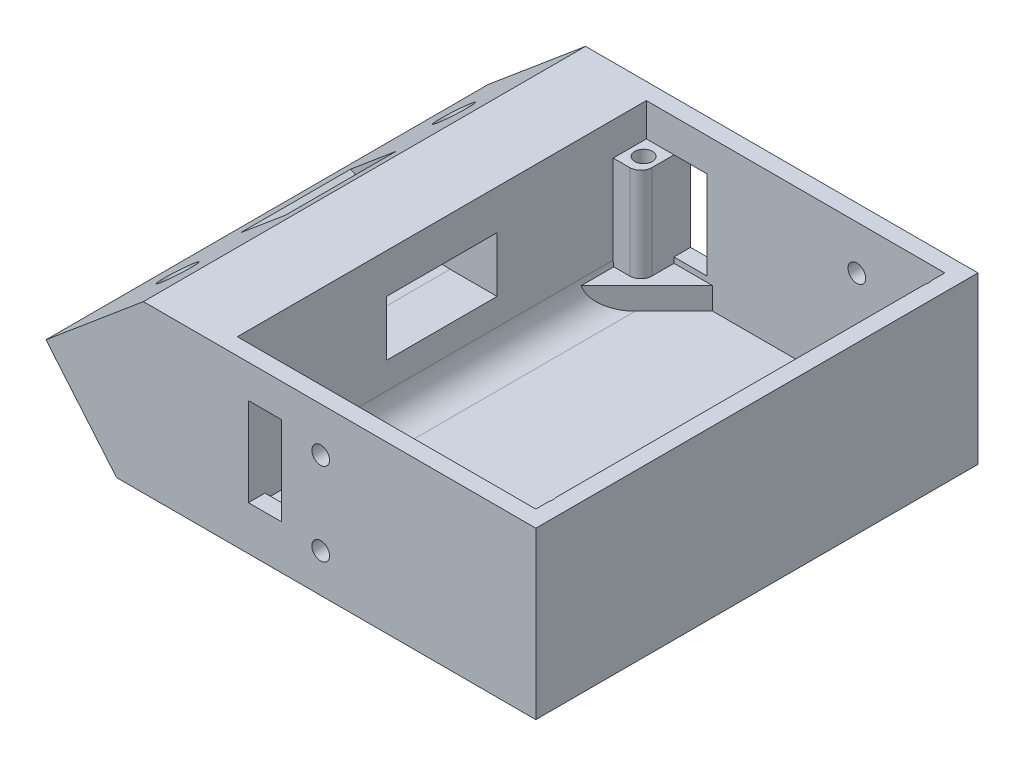
SolidWorks part; units mm, degrees
ref_plane "Спереди" through (0, 0, 0) normal (0, 0, 1) x (1, 0, 0)
ref_plane "Сверху" through (0, 0, 0) normal (0, 1, 0) x (1, 0, 0)
ref_plane "Справа" through (0, 0, 0) normal (1, 0, 0) x (0, 0, -1)
sketch "Sketch1" plane through (0, 0, 0) normal (0, 1, 0) x (1, 0, 0)
  line L1 (30.5, -40) -> (-30.5, -40)
  line L2 (30.5, -40) -> (30.5, 40)
  line L3 (30.5, 40) -> (-30.5, 40)
  line L4 (-30.5, -40) -> (-30.5, 40)
  line L5 (30.5, -40) -> (-30.5, 40) construction
  line L6 (30.5, 40) -> (-30.5, -40) construction
  point P0 (0, 0)
  dimension "D1" = 80
  dimension "D2" = 61
extrude "Boss-Extrude1" add sketch "Sketch1" along normal blind 30
sketch "Sketch2" plane through (0, 30, 0) normal (0, 1, 0) x (1, 0, 0)
  line L0 (30.5, 40) -> (-30.5, 40) construction
  line L1 (-26.5, -37) -> (27.5, -37)
  line L2 (-26.5, -37) -> (-26.5, 37)
  line L3 (-26.5, 37) -> (27.5, 37)
  line L4 (27.5, -37) -> (27.5, 37)
  line L5 (-30.5, -40) -> (30.5, -40) construction
  line L6 (-30.5, 40) -> (-30.5, -40) construction
  line L7 (30.5, -40) -> (30.5, 40) construction
  point P0 (0, 0)
  dimension "D1" = 3
  dimension "D2" = 3
  dimension "D3" = 3
  dimension "D4" = 4
extrude "Cut-Extrude1" cut sketch "Sketch2" against normal blind 27
sketch "Sketch11" plane through (0, 0, 40) normal (0, 0, 1) x (1, 0, 0)
  line L0 (-30.5, 30) -> (-40.5, 30)
  line L1 (-30.5, 0) -> (-58.119, 0)
  line L2 (-30.5, 0) -> (-30.5, 30)
  line L3 (-58.119, 0) -> (-58.119, 15.2159)
  line L4 (-40.5, 30) -> (-58.119, 15.2159)
  line L5 (-40.5, 30) -> (-40.5, 0) construction
  dimension "D1" = 23
  dimension "D2" = 50
  dimension "D3" = 10
extrude "Boss-Extrude3" add sketch "Sketch11" against normal up to surface (80 mm away) up to face at (0, 15, -40)
sketch "Sketch7" plane through (0, 3, 0) normal (0, 1, 0) x (1, 0, 0)
  line L0 (27.5, -25) -> (15.5, -37)
  line L1 (27.5, -37) -> (27.5, 37) construction
  line L2 (-26.5, -37) -> (27.5, -37) construction
  line L3 (15.5, -37) -> (27.5, -37)
  line L4 (27.5, -37) -> (27.5, -25)
  line L5 (27.5, 25) -> (15.5, 37)
  line L6 (27.5, 37) -> (-26.5, 37) construction
  line L7 (15.5, 37) -> (27.5, 37)
  line L8 (27.5, 37) -> (27.5, 25)
  line L9 (-26.5, 25) -> (-14.5, 37)
  line L10 (-26.5, 37) -> (-26.5, -37) construction
  line L11 (-14.5, 37) -> (-26.5, 37)
  line L12 (-26.5, 37) -> (-26.5, 25)
  line L13 (-14.5, -37) -> (-26.5, -25)
  line L14 (-26.5, 37) -> (-26.5, -37) construction
  line L15 (-26.5, -25) -> (-26.5, -37)
  line L16 (-26.5, -37) -> (-14.5, -37)
  dimension "D1" = 12
extrude "Boss-Extrude2" add sketch "Sketch7" along normal blind 4
sketch "Sketch5" plane through (0, 0, 0) normal (0, -1, 0) x (1, 0, 0)
  line L0 (1, -40) -> (1, 40) construction
  line L1 (30.5, -40) -> (-58.119, -40) construction
  line L2 (-58.119, 40) -> (30.5, 40) construction
  line L4 (26, 34) -> (-24, 34) construction
  line L5 (26, 34) -> (26, -34) construction
  line L6 (26, -34) -> (-24, -34) construction
  line L7 (-24, 34) -> (-24, -34) construction
  line L8 (26, 34) -> (-24, -34) construction
  line L9 (26, -34) -> (-24, 34) construction
  circle A0 centre (-24, -34) radius 1.6
  circle A1 centre (-24, 34) radius 1.6
  circle A2 centre (26, 34) radius 1.6
  circle A3 centre (26, -34) radius 1.6
  point P6 (1, 0)
  dimension "D4" = 3.2
  dimension "D1" = 68
  dimension "D2" = 50
  dimension "D3" = 1
extrude "Cut-Extrude3" cut sketch "Sketch5" against normal through all
sketch "Sketch8" plane through (0, 0, 0) normal (0, -1, 0) x (1, 0, 0)
  line L0 (30.5, -40) -> (-58.119, -40) construction
  line L1 (-25.625, 36.8146) -> (-27.25, 34)
  line L2 (-27.25, 34) -> (-25.625, 31.1854)
  line L3 (-25.625, 31.1854) -> (-22.375, 31.1854)
  line L4 (-22.375, 31.1854) -> (-20.75, 34)
  line L5 (-20.75, 34) -> (-22.375, 36.8146)
  line L6 (-22.375, 36.8146) -> (-25.625, 36.8146)
  line L7 (24.375, 36.8146) -> (22.75, 34)
  line L8 (22.75, 34) -> (24.375, 31.1854)
  line L9 (24.375, 31.1854) -> (27.625, 31.1854)
  line L10 (27.625, 31.1854) -> (29.25, 34)
  line L11 (29.25, 34) -> (27.625, 36.8146)
  line L12 (27.625, 36.8146) -> (24.375, 36.8146)
  line L13 (-25.625, -31.1854) -> (-27.25, -34)
  line L14 (-27.25, -34) -> (-25.625, -36.8146)
  line L15 (-25.625, -36.8146) -> (-22.375, -36.8146)
  line L16 (-22.375, -36.8146) -> (-20.75, -34)
  line L17 (-20.75, -34) -> (-22.375, -31.1854)
  line L18 (-22.375, -31.1854) -> (-25.625, -31.1854)
  line L19 (24.375, -31.1854) -> (22.75, -34)
  line L20 (22.75, -34) -> (24.375, -36.8146)
  line L21 (24.375, -36.8146) -> (27.625, -36.8146)
  line L22 (27.625, -36.8146) -> (29.25, -34)
  line L23 (29.25, -34) -> (27.625, -31.1854)
  line L24 (27.625, -31.1854) -> (24.375, -31.1854)
  circle A0 centre (-24, 34) radius 3.25 construction
  circle A1 centre (26, 34) radius 3.25 construction
  circle A2 centre (-24, -34) radius 3.25 construction
  circle A3 centre (26, -34) radius 3.25 construction
  dimension "D1" = 6.5
extrude "Cut-Extrude4" cut sketch "Sketch8" against normal blind 3
sketch "Sketch12" plane through (0, 0, 40) normal (0, 0, 1) x (1, 0, 0)
  line L0 (-58.119, 15.2159) -> (-45.3514, 0)
  line L1 (-58.119, 0) -> (30.5, 0) construction
  line L2 (-45.3514, 0) -> (-58.119, 0)
  line L3 (-58.119, 0) -> (-58.119, 15.2159)
  line L4 (-40.5, 30) -> (-58.119, 15.2159) construction
extrude "Cut-Extrude6" cut sketch "Sketch12" against normal through all
sketch "Sketch16" plane through (-31.5057, 37.5471, 0) normal (-0.6428, 0.766, 0) x (0.766, 0.6428, 0)
  line L0 (-23.2412, 40) -> (-23.2412, -40) construction
  line L1 (-34.7412, 40) -> (-11.7412, 40) construction
  line L2 (-11.7412, -40) -> (-34.7412, -40) construction
  circle A0 centre (-23.2412, 25) radius 3.1
  circle A1 centre (-23.2412, -25) radius 3.1
  point P10 (-23.2412, 0)
  dimension "D1" = 6.2
  dimension "D2" = 50
  dimension "D3" = 25
extrude "Cut-Extrude8" cut sketch "Sketch16" against normal through all
fillet "Fillet1" radius 5 1 edges at (-26.5, 3, 0)
sketch "Sketch17" plane through (-31.5057, 37.5471, 0) normal (-0.6428, 0.766, 0) x (0.766, 0.6428, 0)
  circle A0 centre (-23.2412, -25) radius 6.5
  circle A1 centre (-23.2412, 25) radius 6.5
  dimension "D2" = 13
extrude "Cut-Extrude9" cut sketch "Sketch17" against normal blind 10 from offset 25 offset against normal yes
sketch "Sketch18" plane through (0, 0, 40) normal (0, 0, 1) x (1, 0, 0)
  line L0 (-44.8128, 26.3811) -> (-37.8032, 22.8149)
  line L2 (-40.5, 30) -> (-58.119, 15.2159) construction
  line L3 (-37.8032, 22.8149) -> (-23.8032, 22.8149)
  line L4 (-23.8032, 22.8149) -> (-23.8032, 12.8149)
  line L5 (-23.8032, 12.8149) -> (-39.8032, 12.8149)
  line L6 (-39.8032, 12.8149) -> (-52.9869, 19.5222)
  line L7 (-52.9869, 19.5222) -> (-44.8128, 26.3811)
  dimension "D1" = 10
  dimension "D2" = 14
  dimension "D3" = 16
extrude "Cut-Extrude10" cut sketch "Sketch18" against normal blind 20 from offset 30 offset against normal yes
fillet "Fillet2" radius 20 2 edges at (-39.8032, 12.8149, 0) (-37.8032, 22.8149, 0)
sketch "Sketch19" plane through (0, 0, 40) normal (0, 0, 1) x (1, 0, 0)
  line L0 (-45.3514, 0) -> (-8.4162, 0) construction
  line L1 (-45.3514, 0) -> (30.5, 0) construction
  line L2 (-8.4162, -0.4537) -> (-8.4162, 30) construction
  line L3 (-40.5, 30) -> (30.5, 30) construction
  circle A0 centre (-8.4162, 22) radius 1.6
  circle A1 centre (-8.4162, 7) radius 1.6
  dimension "D2" = 3.2
  dimension "D3" = 15
  dimension "D1" = 36.9352
  dimension "D4" = 8
extrude "Cut-Extrude11" cut sketch "Sketch19" against normal up to next
sketch "Sketch20" plane through (0, 0, 37) normal (0, 0, -1) x (-1, 0, 0)
  line L0 (21.5, 8) -> (21.5, 24)
  line L2 (21.5, 24) -> (15.5, 24)
  line L3 (15.5, 24) -> (15.5, 8)
  line L4 (15.5, 8) -> (21.5, 8)
  line L5 (40.5, 30) -> (-30.5, 30) construction
  line L6 (26.5, 8) -> (26.5, 30) construction
  line L7 (26.5, 8) -> (-6.3924, 8) construction
  dimension "D1" = 6
  dimension "D2" = 6
  dimension "D3" = 5
extrude "Cut-Extrude12" cut sketch "Sketch20" along normal through all both and the other way through all
sketch "Sketch21" plane through (0, 7, 0) normal (0, 1, 0) x (1, 0, 0)
  line L0 (-26.5, -37) -> (-26.5, 37) construction
  line L1 (-21.5, -31) -> (-26.5, -31)
  line L2 (-21.5, -31) -> (-21.5, -37)
  line L3 (-21.5, -37) -> (-26.5, -37)
  line L4 (-26.5, -31) -> (-26.5, -37)
  line L5 (-21.5, -31) -> (-26.5, -37) construction
  line L6 (-21.5, -37) -> (-26.5, -31) construction
  line L7 (-26.399, -37) -> (-14.5, -37) construction
  line L8 (-14.5, 37) -> (-26.399, 37) construction
  line L9 (-26.5, 31) -> (-21.5, 31)
  line L10 (-26.5, 31) -> (-26.5, 37)
  line L11 (-26.5, 37) -> (-21.5, 37)
  line L12 (-21.5, 31) -> (-21.5, 37)
  line L13 (-26.5, 31) -> (-21.5, 37) construction
  line L14 (-26.5, 37) -> (-21.5, 31) construction
  line L15 (27.5, 37) -> (15.5, 37) construction
  line L16 (29, 31) -> (23, 31)
  line L17 (29, 31) -> (29, 37)
  line L18 (29, 37) -> (23, 37)
  line L19 (23, 31) -> (23, 37)
  line L20 (29, 31) -> (23, 37) construction
  line L21 (29, 37) -> (23, 31) construction
  line L22 (15.5, -37) -> (27.5, -37) construction
  line L23 (29, -31) -> (23, -31)
  line L24 (29, -31) -> (29, -37)
  line L25 (29, -37) -> (23, -37)
  line L26 (23, -31) -> (23, -37)
  line L27 (29, -31) -> (23, -37) construction
  line L28 (29, -37) -> (23, -31) construction
  circle A0 centre (-24, -34) radius 1.6
  circle A1 centre (-24, -34) radius 1.6 construction
  circle A2 centre (-24, 34) radius 1.6
  circle A3 centre (-24, 34) radius 1.6 construction
  circle A4 centre (26, 34) radius 1.6
  arc A5 (27.5, 34.5568) -> (27.5, 33.4432) centre (26, 34) ccw construction
  circle A6 centre (26, -34) radius 1.6
  arc A7 (27.5, -33.4432) -> (27.5, -34.5568) centre (26, -34) ccw construction
  point P0 (-24, -34)
  point P14 (-24, 34)
  point P26 (26, 34)
  point P39 (26, -34)
  dimension "D1" = 6
extrude "Boss-Extrude4" add sketch "Sketch21" along normal up to surface (17 mm away) up to face at (-18.5, 24, 38.5)
fillet "Fillet4" radius 2 4 edges at (23, 15.5, -31) (23, 15.5, 31) (-21.5, 15.5, 31) (-21.5, 15.5, -31)
sketch "Sketch22" plane through (0, 0, 40) normal (0, 0, 1) x (1, 0, 0)
  line L0 (-8.4162, 22) -> (11.5838, 22) construction
  line L1 (-8.4162, 7) -> (11.5838, 7) construction
  line L2 (11.5838, 7) -> (11.5838, 22) construction
  circle A0 centre (11.5838, 22) radius 1.6
  circle A1 centre (11.5838, 7) radius 1.6
  circle A2 centre (-8.4162, 22) radius 1.6 construction
  dimension "D1" = 20
extrude "Cut-Extrude13" cut sketch "Sketch22" against normal through all from surface at -77 starting at face at (-3.0333, 15.3333, -37)
